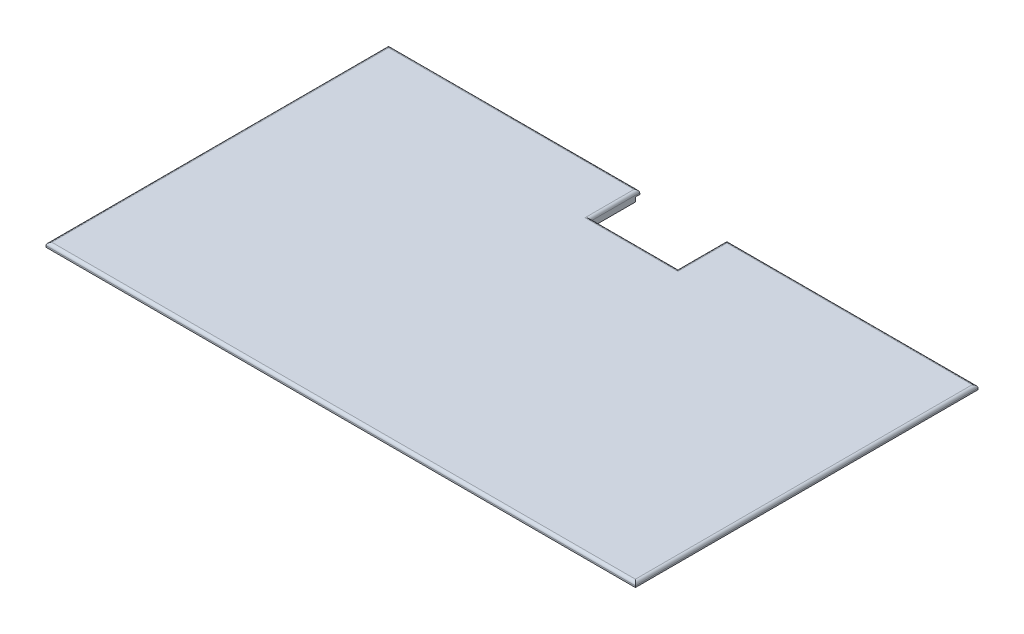
SolidWorks part; units mm, degrees
ref_plane "前视基准面" through (0, 0, 0) normal (0, 0, 1) x (1, 0, 0)
ref_plane "上视基准面" through (0, 0, 0) normal (0, 1, 0) x (1, 0, 0)
ref_plane "右视基准面" through (0, 0, 0) normal (1, 0, 0) x (0, 0, -1)
other "Configuration Table"
sketch "草图1" plane through (0, 0, 0) normal (0, 1, 0) x (1, 0, 0)
  line L1 (-100, -57.5) -> (100, -57.5)
  line L2 (-100, -57.5) -> (-100, 57.5)
  line L3 (-100, 57.5) -> (100, 57.5)
  line L4 (100, -57.5) -> (100, 57.5)
  line L5 (-100, -57.5) -> (100, 57.5) construction
  line L6 (-100, 57.5) -> (100, -57.5) construction
  point P0 (0, 0)
  dimension "D1" = 115
  dimension "D2" = 200
extrude "凸台-拉伸1" add sketch "草图1" along normal blind 1.5
ref_plane "基准面1" through (0, 1.5, 0) normal (0, 1, 0) x (1, 0, 0)
sketch "草图2" plane through (0, 1.5, 0) normal (0, 1, 0) x (1, 0, 0)
  line L0 (100, -57.5) -> (100, 57.5) construction
  line L1 (100, 57.5) -> (-100, 57.5) construction
  line L2 (100, -57.5) -> (100, 57.5) construction
  line L3 (100, 57.5) -> (-100, 57.5) construction
  line L21 (-101.5, -59) -> (101.5, -59)
  line L22 (-101.5, -59) -> (-101.5, 59)
  line L23 (-101.5, 59) -> (101.5, 59)
  line L24 (101.5, -59) -> (101.5, 59)
  line L25 (-101.5, -59) -> (101.5, 59) construction
  line L26 (-101.5, 59) -> (101.5, -59) construction
  point P2 (0, 0)
  dimension "D1" = 1.5
  dimension "D2" = 1.5
extrude "凸台-拉伸2" add sketch "草图2" along normal blind 1.5
sketch "草图3" plane through (0, 0, 0) normal (0, -1, 0) x (1, 0, 0)
  line L0 (0, 0) -> (0, -57.5) construction
  line L1 (100, -57.5) -> (-100, -57.5) construction
  line L3 (-15, -42.148) -> (15, -42.148)
  line L4 (-15, -42.148) -> (-15, -60.6209)
  line L5 (-15, -60.6209) -> (15, -60.6209)
  line L6 (15, -42.148) -> (15, -60.6209)
  line L7 (-15, -42.148) -> (15, -60.6209) construction
  line L8 (-15, -60.6209) -> (15, -42.148) construction
  point P5 (0, -51.3844)
  dimension "D2" = 30
extrude "切除-拉伸1" cut sketch "草图3" against normal blind 11.5
fillet "圆角3" radius 1 8 edges at (0, 3, 59) (-101.5, 3, 0) (58.25, 3, -59) (-58.25, 3, -59) (101.5, 3, 0) (-15, 3, -50.574) (0, 3, -42.148) (15, 3, -50.574)
